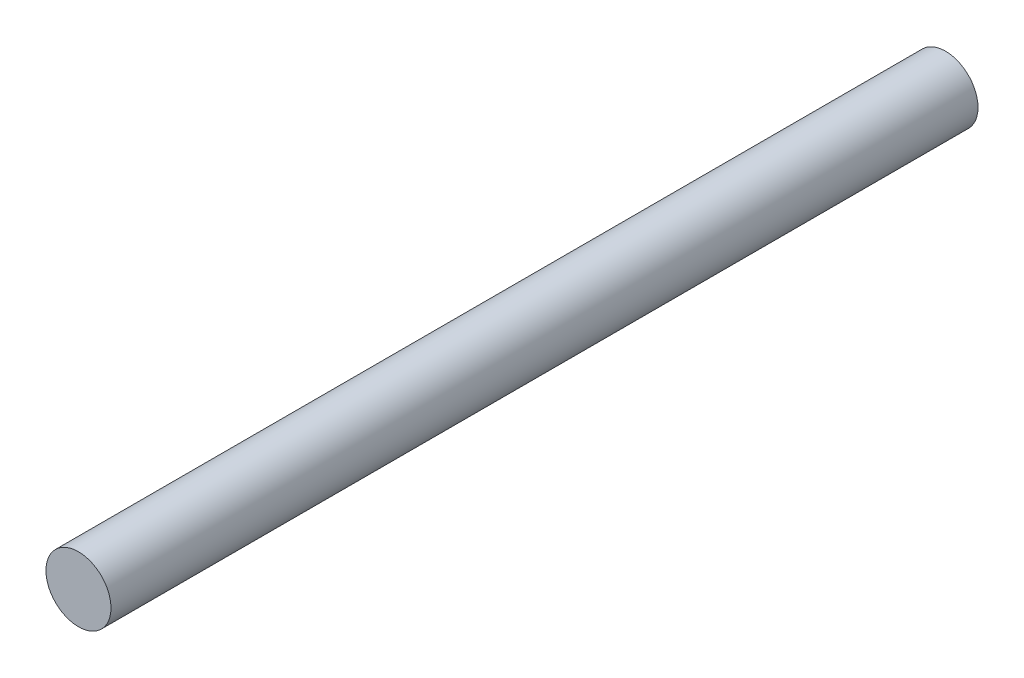
SolidWorks part; units mm, degrees
ref_plane "Спереди" through (0, 0, 0) normal (0, 0, 1) x (1, 0, 0)
ref_plane "Сверху" through (0, 0, 0) normal (0, 1, 0) x (1, 0, 0)
ref_plane "Справа" through (0, 0, 0) normal (1, 0, 0) x (0, 0, -1)
sketch "Эскиз1" plane through (0, 0, 0) normal (0, 0, 1) x (1, 0, 0)
  circle A0 centre (0, 0) radius 4.5
extrude "Бобышка-Вытянуть1" add sketch "Эскиз1" along normal blind 120
